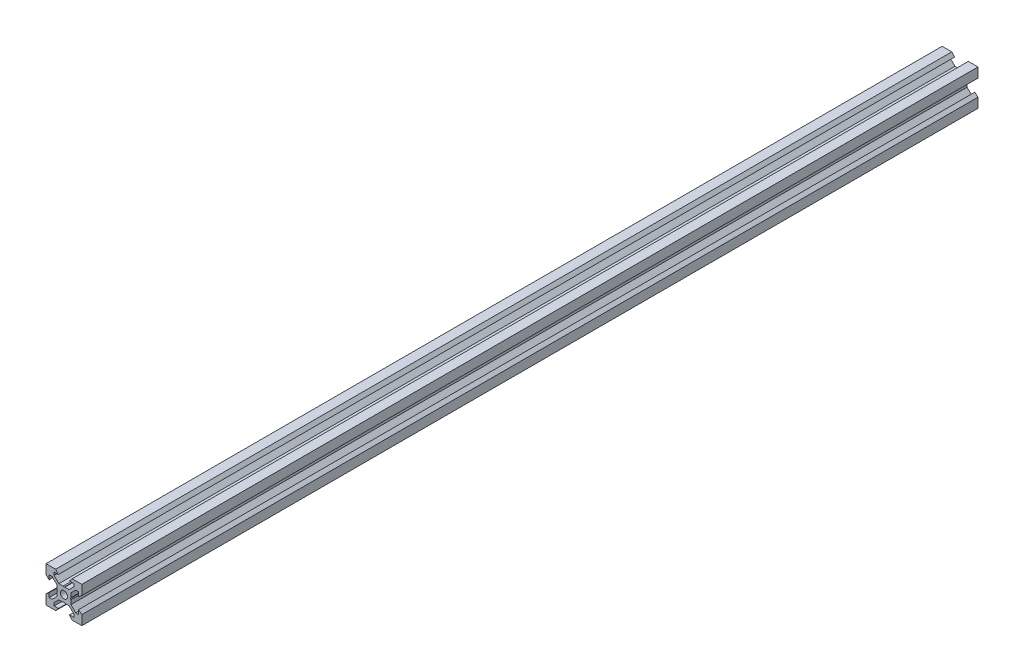
SolidWorks part; units mm, degrees
ref_plane "Front Plane" through (0, 0, 0) normal (0, 0, 1) x (1, 0, 0)
ref_plane "Top Plane" through (0, 0, 0) normal (0, 1, 0) x (1, 0, 0)
ref_plane "Right Plane" through (0, 0, 0) normal (1, 0, 0) x (0, 0, -1)
sketch "Sketch1" plane through (0, 0, 0) normal (0, 0, 1) x (1, 0, 0)
  line L0 (10, 10) -> (4.6104, 10) construction
  line L1 (10, 10) -> (10, 4.6104) construction
  line L2 (10, -10) -> (10, -4.6104) construction
  line L3 (10, -10) -> (4.6104, -10) construction
  line L4 (10, 10) -> (10, 4.6104)
  line L5 (6.5607, 5.5) -> (8.2, 5.5)
  line L6 (5.5, 8.2) -> (5.5, 6.5607)
  line L7 (10, 10) -> (4.6104, 10)
  line L8 (10, 10) -> (10, 4.6104)
  line L9 (6.5607, 5.5) -> (3.9, 2.8393)
  line L10 (5.5, 6.5607) -> (2.8393, 3.9)
  line L11 (10, 4.6104) -> (8.2, 3.1)
  line L12 (4.6104, 10) -> (3.1, 8.2)
  line L13 (8.2, 3.1) -> (8.2, 5.5)
  line L14 (3.1, 8.2) -> (5.5, 8.2)
  line L15 (-6.5607, 5.5) -> (-8.2, 5.5)
  line L16 (6.5607, -5.5) -> (8.2, -5.5)
  line L17 (3.1, -8.2) -> (5.5, -8.2)
  line L18 (8.2, -3.1) -> (8.2, -5.5)
  line L19 (4.6104, -10) -> (3.1, -8.2)
  line L20 (10, -4.6104) -> (8.2, -3.1)
  line L21 (0.5196, -3.9) -> (0, -3.6)
  line L22 (0.5196, 3.9) -> (0, 3.6)
  line L23 (3.6, 0) -> (3.9, -0.5196)
  line L24 (3.9, 0.5196) -> (3.6, 0)
  line L25 (3.9, 0.5196) -> (3.9, 2.8393)
  line L26 (2.8393, 3.9) -> (0.5196, 3.9)
  line L27 (3.9, -2.8393) -> (3.9, -0.5196)
  line L28 (2.8393, -3.9) -> (0.5196, -3.9)
  line L29 (5.5, -6.5607) -> (2.8393, -3.9)
  line L30 (6.5607, -5.5) -> (3.9, -2.8393)
  line L31 (10, -10) -> (10, -4.6104)
  line L32 (10, -10) -> (4.6104, -10)
  line L33 (5.5, -8.2) -> (5.5, -6.5607)
  line L34 (-6.5607, -5.5) -> (-8.2, -5.5)
  line L35 (10, -10) -> (10, -4.6104)
  line L36 (0, 0) -> (0, 8.2) construction
  line L37 (-10, -10) -> (-4.6104, -10) construction
  line L38 (-10, -10) -> (-10, -4.6104) construction
  line L39 (-10, 10) -> (-10, 4.6104) construction
  line L40 (-10, 10) -> (-4.6104, 10) construction
  line L41 (-10, -10) -> (-10, -4.6104)
  line L43 (-5.5, -8.2) -> (-5.5, -6.5607)
  line L44 (-10, -10) -> (-4.6104, -10)
  line L45 (-10, -10) -> (-10, -4.6104)
  line L46 (-6.5607, -5.5) -> (-3.9, -2.8393)
  line L47 (-5.5, -6.5607) -> (-2.8393, -3.9)
  line L48 (-2.8393, -3.9) -> (-0.5196, -3.9)
  line L49 (-3.9, -2.8393) -> (-3.9, -0.5196)
  line L50 (-2.8393, 3.9) -> (-0.5196, 3.9)
  line L51 (-3.9, 0.5196) -> (-3.9, 2.8393)
  line L52 (-3.9, 0.5196) -> (-3.6, 0)
  line L53 (-3.6, 0) -> (-3.9, -0.5196)
  line L54 (-0.5196, 3.9) -> (0, 3.6)
  line L55 (-0.5196, -3.9) -> (0, -3.6)
  line L56 (-10, -4.6104) -> (-8.2, -3.1)
  line L57 (-4.6104, -10) -> (-3.1, -8.2)
  line L58 (-8.2, -3.1) -> (-8.2, -5.5)
  line L59 (-3.1, -8.2) -> (-5.5, -8.2)
  line L60 (-10, -10) -> (10, -10) construction
  line L61 (-10, -10) -> (-10, 10) construction
  line L62 (-3.1, 8.2) -> (-5.5, 8.2)
  line L63 (-8.2, 3.1) -> (-8.2, 5.5)
  line L64 (-4.6104, 10) -> (-3.1, 8.2)
  line L65 (-10, 4.6104) -> (-8.2, 3.1)
  line L66 (-5.5, 6.5607) -> (-2.8393, 3.9)
  line L67 (-6.5607, 5.5) -> (-3.9, 2.8393)
  line L68 (-10, 10) -> (-10, 4.6104)
  line L69 (-10, 10) -> (-4.6104, 10)
  line L70 (-5.5, 8.2) -> (-5.5, 6.5607)
  line L71 (-10, 10) -> (10, 10) construction
  line L72 (-10, 10) -> (-10, 4.6104)
  line L73 (10, -10) -> (10, 10) construction
  line L74 (-10, -10) -> (10, 10) construction
  line L75 (-10, 10) -> (10, -10) construction
  circle A0 centre (0, 0) radius 2
  dimension "D7" = 4
  dimension "D1" = 20
  dimension "D2" = 5.3896
  dimension "D3" = 4.5
  dimension "D4" = 50
  dimension "D5" = 1.8
  dimension "D6" = 1.5104
  dimension "D8" = 5.5
  dimension "D9" = 120
  dimension "D10" = 0.3
  dimension "D11" = 2.3197
  dimension "D12" = 7.8
  dimension "D13" = 7.8
  dimension "D14" = 1.5
  dimension "D15" = 2.6607
extrude "Boss-Extrude1" add sketch "Sketch1" along normal mid plane 500 contours L70 L62 L64 L69 L68 L65 L63 L15 L67 L51 L52 L53 L49 L46 L34 L58 L56 L41 L44 L57 L59 L43 L47 L48 L55 L21 L28 L29 L33 L17 L19 L32 L31 L20 L18 L16 L30 L27 L23 L24 L25 L9 L5 L13 L11 L4 L7 L12 L14 L6 L10
